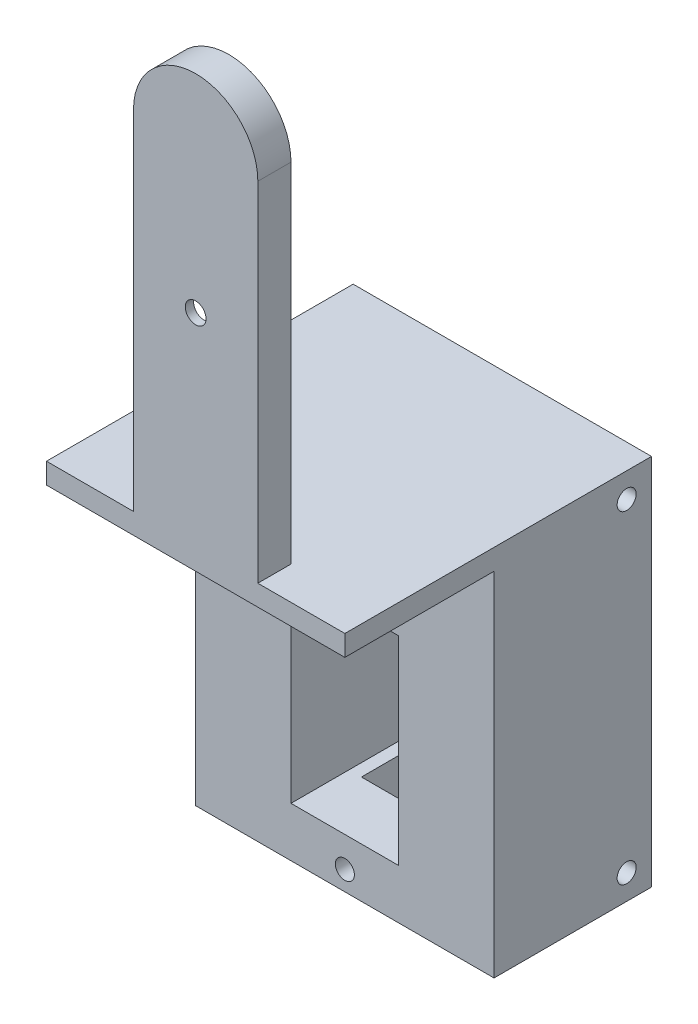
SolidWorks part; units mm, degrees
ref_plane "前基準面" through (0, 0, 0) normal (0, 0, 1) x (1, 0, 0)
ref_plane "上基準面" through (0, 0, 0) normal (0, 1, 0) x (1, 0, 0)
ref_plane "右基準面" through (0, 0, 0) normal (1, 0, 0) x (0, 0, -1)
sketch "草圖1" plane through (0, 0, 0) normal (0, 0, 1) x (1, 0, 0)
  line L1 (7.5, 10) -> (7.5, 52)
  line L3 (-7.5, 10) -> (-7.5, 52)
  line L4 (7.5, 10) -> (-7.5, 10)
  arc A0 (7.5, 52) -> (-7.5, 52) centre (0, 52) ccw
  dimension "D1" = 15
  dimension "D2" = 7.5
  dimension "D3" = 42
extrude "填料-伸長1" add sketch "草圖1" along normal blind 4
sketch "草圖3" plane through (0, 0, 0) normal (0, 0, 1) x (1, 0, 0)
  line L0 (0, 0) -> (0, 14.8578) construction
  line L1 (7.5, 52) -> (-7.5, 52) construction
  line L2 (7.5, 15) -> (-7.5, 15) construction
  line L3 (7.5, 10) -> (7.5, 52) construction
  line L4 (-7.5, 52) -> (-7.5, 10) construction
  line L6 (7.5, 34.5) -> (5, 34.5) construction
  line L7 (5, 34.5) -> (2.1147, 16.658)
  line L8 (5, 34.5) -> (2.1328, 52)
  line L9 (-2.1328, 52) -> (-5, 34.5)
  line L10 (-5, 34.5) -> (-2.1422, 17)
  line L11 (0, 54.1328) -> (0, 59.5) construction
  line L12 (-5, 34.5) -> (-7.5, 34.5) construction
  arc A0 (7.5, 52) -> (-7.5, 52) centre (0, 52) ccw construction
  arc A1 (-4.7386, 36.0956) -> (-4.7403, 32.9094) centre (0, 34.5) ccw
  arc A2 (-2.1422, 17) -> (2.1147, 16.658) centre (0, 17) ccw
  arc A3 (-2.1328, 52) -> (2.1328, 52) centre (0, 52) cw
  arc A4 (4.7452, 32.9241) -> (4.7386, 36.0956) centre (0, 34.5) ccw
  dimension "D4" = 10
  dimension "D1" = 35
  dimension "D2" = 4.2656
  dimension "D3" = 4.257
extrude "除料-伸長1" cut sketch "草圖3" along normal blind 3 contours A3 L9 L10 A2 L7 L8
sketch "草圖5" plane through (0, 0, 0) normal (0, 0, 1) x (1, 0, 0)
  line L0 (5, 34.5) -> (-5, 34.5) construction
  circle A0 centre (0, 34.5) radius 1.25
  dimension "D1" = 2.5
extrude "除料-伸長2" cut sketch "草圖5" along normal blind 12.4
ref_plane "平面1" through (0, -35, 0) normal (0, 1, 0) x (1, 0, 0)
sketch "草圖13" plane through (0, 0, 4) normal (0, 0, 1) x (1, 0, 0)
  line L0 (0, 10) -> (0, -4.3971) construction
  line L1 (7.5, 10) -> (-7.5, 10) construction
  line L3 (-18, 10) -> (18, 10)
  line L4 (-18, 10) -> (-18, -35)
  line L5 (-18, -35) -> (18, -35)
  line L6 (18, 10) -> (18, -35)
  dimension "D1" = 45
  dimension "D2" = 45
  dimension "D3" = 18
  dimension "D4" = 18
ref_plane "平面2" through (0, 0, 4) normal (0, 0, 1) x (1, 0, 0)
extrude "填料-伸長2" add sketch "草圖13" against normal blind 37
sketch "草圖14" plane through (0, 0, 4) normal (0, 0, -1) x (-1, 0, 0)
  line L0 (0, 10) -> (0, -35) construction
  line L1 (-7.5, 10) -> (7.5, 10) construction
  line L2 (18, -35) -> (-18, -35) construction
  line L4 (-6.5, -5) -> (6.5, -5)
  line L5 (-6.5, -5) -> (-6.5, -29)
  line L6 (-6.5, -29) -> (6.5, -29)
  line L7 (6.5, -5) -> (6.5, -29)
  point P10 (0, -12.5)
  dimension "D1" = 6.5
  dimension "D2" = 6.5
  dimension "D3" = 24
  dimension "D4" = 6
ref_plane "平面4" through (0, 0, 4) normal (0, 0, 1) x (1, 0, 0)
extrude "除料-伸長3" cut sketch "草圖14" along normal blind 35
sketch "草圖15" plane through (0, 0, 4) normal (0, 0, 1) x (1, 0, 0)
  line L0 (0, -5) -> (0, -22.6416) construction
  line L1 (-6.5, -5) -> (6.5, -5) construction
  line L2 (0, -1.85) -> (0, -32.65) construction
  line L4 (6.5, -29) -> (-6.5, -29) construction
  circle A0 centre (0, -1.85) radius 1.15
  circle A1 centre (0, -32.65) radius 1.15
  dimension "D1" = 2.3
  dimension "D2" = 2.3
  dimension "D3" = 2
  dimension "D4" = 2.5
extrude "除料-伸長4" cut sketch "草圖15" against normal blind 31
ref_plane "平面5" through (0, -35, 0) normal (0, -1, 0) x (-1, 0, 0)
sketch "草圖16" plane through (0, -35, 0) normal (0, -1, 0) x (-1, 0, 0)
  line L0 (0, 33) -> (0, 0) construction
  line L1 (18, 33) -> (-18, 33) construction
  line L3 (-5, 29) -> (5, 29)
  line L4 (-5, 29) -> (-5, 21)
  line L5 (-5, 21) -> (5, 21)
  line L6 (5, 29) -> (5, 21)
  dimension "D1" = 10
  dimension "D2" = 4
  dimension "D3" = 8
  dimension "D4" = 5
extrude "除料-伸長5" cut sketch "草圖16" against normal blind 8
sketch "草圖17" plane through (0, 0, 4) normal (0, 0, 1) x (1, 0, 0)
  line L0 (-18, 10) -> (-18, -35) construction
  line L1 (-18, 7.5) -> (18, 7.5)
  line L2 (-18, 7.5) -> (-18, -35)
  line L3 (-18, -35) -> (18, -35)
  line L4 (18, 7.5) -> (18, -35)
  line L5 (-10.45, -35) -> (10.45, -35) construction
  line L6 (18, -35) -> (18, 10) construction
  line L7 (7.5, 10) -> (-7.5, 10) construction
  dimension "D1" = 2.5
extrude "除料-伸長6" cut sketch "草圖17" against normal blind 18
sketch "草圖23" plane through (-18, 0, 0) normal (-1, 0, 0) x (0, 0, 1)
  line L0 (-33, 10) -> (-33, -35) construction
  line L1 (-33, 10) -> (4, 10) construction
  line L2 (-10.45, -35) -> (10.45, -35) construction
  circle A0 centre (-30, 7) radius 1.15
  circle A1 centre (-30, -32) radius 1.15
  dimension "D5" = 2.3
  dimension "D6" = 2.3
  dimension "D1" = 3
  dimension "D2" = 3
  dimension "D3" = 3
  dimension "D4" = 3
extrude "除料-伸長7" cut sketch "草圖23" against normal blind 5
sketch "草圖24" plane through (18, 0, 0) normal (1, 0, 0) x (0, 0, -1)
  line L0 (33, 10) -> (-4, 10) construction
  line L1 (33, -35) -> (33, 10) construction
  line L2 (-10.45, -35) -> (10.45, -35) construction
  circle A0 centre (30, 7) radius 1.15
  circle A1 centre (30, -32) radius 1.15
  dimension "D5" = 2.3
  dimension "D6" = 2.3
  dimension "D1" = 3
  dimension "D2" = 3
  dimension "D3" = 3
  dimension "D4" = 3
extrude "除料-伸長8" cut sketch "草圖24" against normal blind 5
